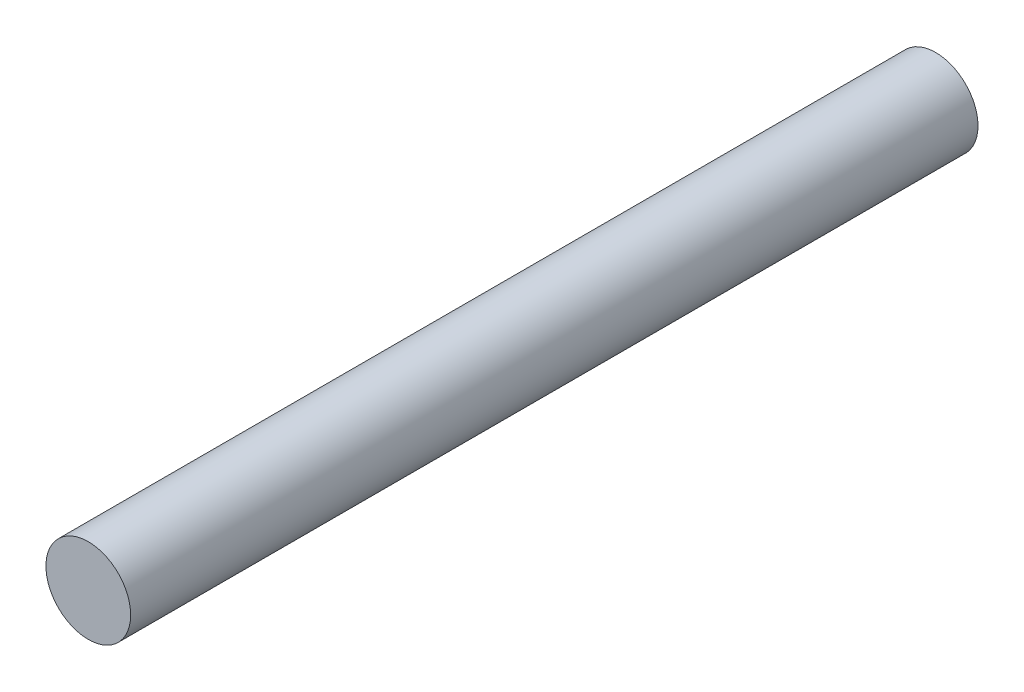
SolidWorks part; units mm, degrees
ref_plane "Alzado" through (0, 0, 0) normal (0, 0, 1) x (1, 0, 0)
ref_plane "Planta" through (0, 0, 0) normal (0, 1, 0) x (1, 0, 0)
ref_plane "Vista lateral" through (0, 0, 0) normal (1, 0, 0) x (0, 0, -1)
sketch "Croquis1" plane through (0, 0, 0) normal (0, 0, 1) x (1, 0, 0)
  circle A0 centre (0, 0) radius 0.6
  dimension "D1" = 1.2
extrude "Saliente-Extruir1" add sketch "Croquis1" along normal blind 12
